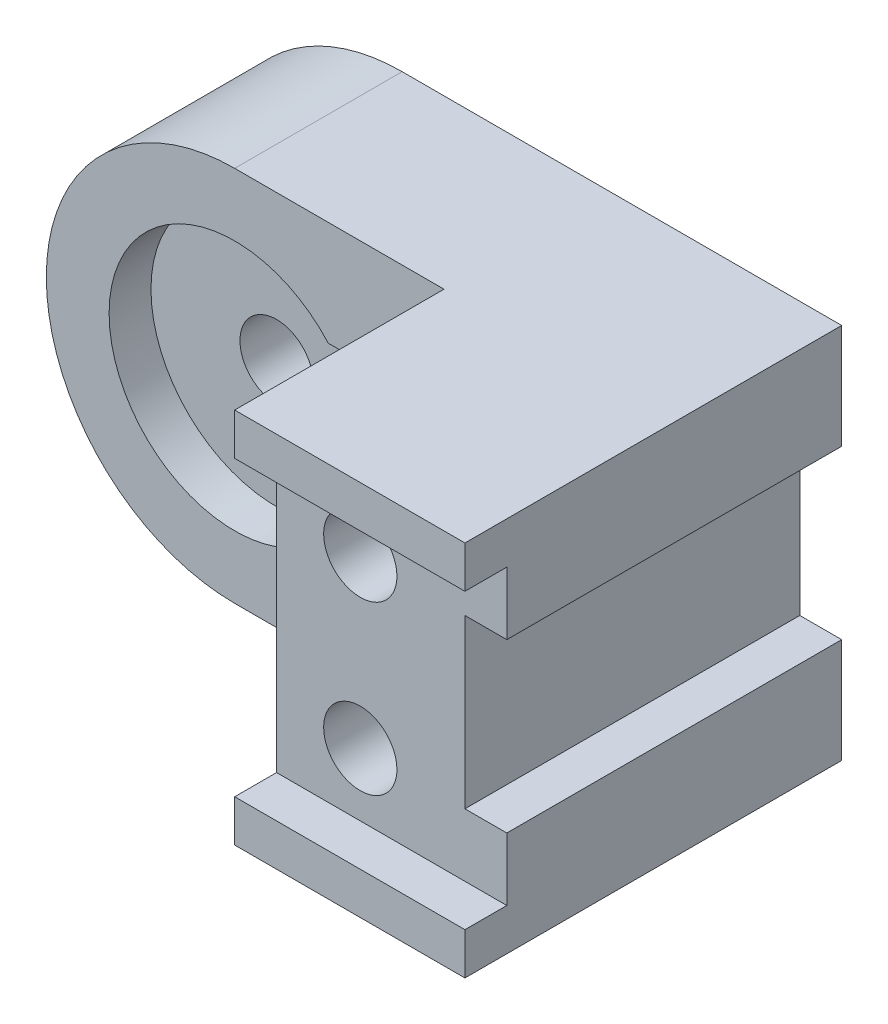
SolidWorks part; units mm, degrees
ref_plane "Front Plane" through (0, 0, 0) normal (0, 0, 1) x (1, 0, 0)
ref_plane "Top Plane" through (0, 0, 0) normal (0, 1, 0) x (1, 0, 0)
ref_plane "Right Plane" through (0, 0, 0) normal (1, 0, 0) x (0, 0, -1)
sketch "Sketch1" plane through (0, 0, 0) normal (0, 0, 1) x (1, 0, 0)
  line L1 (0, 0) -> (150, 0)
  line L2 (0, 0) -> (0, 90)
  line L3 (0, 90) -> (150, 90)
  line L4 (150, 0) -> (150, 90)
  dimension "D1" = 150
  dimension "D2" = 90
extrude "Boss-Extrude1" add sketch "Sketch1" along normal blind 90
sketch "Sketch2" plane through (0, 0, 90) normal (0, 0, 1) x (1, 0, 0)
  line L0 (150, 0) -> (150, 90) construction
  line L1 (150, 65) -> (140, 65)
  line L2 (150, 65) -> (150, 25)
  line L3 (150, 25) -> (140, 25)
  line L4 (140, 65) -> (140, 25)
  dimension "D1" = 10
  dimension "D2" = 40
  dimension "D3" = 25
extrude "Cut-Extrude1" cut sketch "Sketch2" against normal blind 90
sketch "Sketch3" plane through (0, 0, 90) normal (0, 0, 1) x (1, 0, 0)
  line L0 (150, 90) -> (0, 90) construction
  line L1 (45, 90) -> (0, 90)
  line L2 (0, 90) -> (0, 0)
  line L3 (0, 0) -> (45, 0)
  arc A0 (45, 90) -> (45, 0) centre (45, 45) ccw
  line M6 (150, 90) -> (0, 90)
  line M7 (0, 90) -> (0, 0)
  line M8 (0, 0) -> (150, 0)
  dimension "D2" = 45
  dimension "D1" = 45
  dimension "D3" = 45
  dimension "D4" = 45
  dimension "D5" = 90
extrude "Cut-Extrude2" cut sketch "Sketch3" against normal blind 90 contours A0 M6 M7 | A0 L2 M8
sketch "Sketch4" plane through (0, 0, 0) normal (0, 0, -1) x (-1, 0, 0)
  line L0 (-11.459, 75) -> (-45, 75)
  line L1 (-11.459, 15) -> (-45, 15)
  arc A0 (-45, 0) -> (-45, 90) centre (-45, 45) ccw construction
  circle A1 centre (-45, 45) radius 30
  arc M2 (-45, 0) -> (-45, 90) centre (-45, 45) ccw
  dimension "D1" = 15
  dimension "D2" = 15
extrude "Cut-Extrude3" cut sketch "Sketch4" against normal blind 10 contours A1 L1 L0 M2 | A1 L1
sketch "Sketch5" plane through (0, 0, 90) normal (0, 0, 1) x (1, 0, 0)
  line L0 (95, 90) -> (95, 0)
  line L1 (150, 90) -> (45, 90) construction
  line L2 (45, 0) -> (150, 0) construction
  line L3 (95, 0) -> (45, 0)
  line L4 (95, 90) -> (45, 90)
  arc A0 (45, 90) -> (45, 0) centre (45, 45) ccw
  arc A1 (45, 90) -> (45, 0) centre (45, 45) ccw construction
  dimension "D1" = 55
extrude "Cut-Extrude4" cut sketch "Sketch5" against normal blind 50
sketch "Sketch6" plane through (95, 0, 0) normal (-1, 0, 0) x (0, 0, 1)
  line L0 (90, 0) -> (90, 90) construction
  line L1 (90, 80) -> (80, 80)
  line L2 (90, 80) -> (90, 10)
  line L3 (90, 10) -> (80, 10)
  line L4 (80, 80) -> (80, 10)
  dimension "D1" = 10
  dimension "D2" = 10
  dimension "D3" = 10
extrude "Cut-Extrude6" cut sketch "Sketch6" against normal blind 94
sketch "Sketch7" plane through (0, 0, 40) normal (0, 0, 1) x (1, 0, 0)
  line L0 (67.3607, 65) -> (95, 65)
  line L1 (95, 0) -> (95, 90) construction
  line L2 (95, 65) -> (95, 25)
  line L3 (95, 25) -> (67.3607, 25)
  line L4 (45, 0) -> (95, 0) construction
  circle A0 centre (45, 45) radius 30
  line M4 (95, 0) -> (95, 90)
  dimension "D1" = 60
  dimension "D2" = 40
  dimension "D3" = 25
extrude "Cut-Extrude8" cut sketch "Sketch7" against normal blind 10 contours A0 | A0 L3 L0 M4
sketch "Sketch8" plane through (0, 0, 80) normal (0, 0, 1) x (1, 0, 0)
  point P0 (115, 65)
  point P1 (115, 25)
  dimension "D1" = 35
  dimension "D2" = 35
  dimension "D3" = 25
  dimension "D4" = 25
hole_wizard "M20 Tapped Hole2" positions "3DSketch2" profile "Sketch10" tap size "M20" standard "ISO"
sketch3d "3DSketch2"
  point P0 (115, 65, 80)
  point P3 (115, 25, 80)
sketch "Sketch10" plane through (115, 65, 80) normal (1, 0, 0) x (0, -1, 0)
  line L0 (0, 0) -> (0, 30.2575)
  line L1 (0, 30.2575) -> (8.75, 25)
  line L2 (8.75, 25) -> (8.75, 0)
  line L5 (8.75, 0) -> (0, 0)
  line L10 (0, 30.2575) -> (-8.75, 25) construction
  line L11 (0, -6.35) -> (0, 107.95) construction
  dimension "Tap Drill Dia." = 17.5
  dimension "Tap Drill Depth" = 25
  dimension "Drill Angle" = 118
cosmetic thread "Hole Thread3" parameters "D1"=25, "D2"=20
cosmetic thread "Hole Thread4" parameters "D1"=25, "D2"=20
sketch "Sketch11" plane through (0, 0, 30) normal (0, 0, 1) x (1, 0, 0)
  point P0 (45, 45)
hole_wizard "M20 Tapped Hole3" positions "3DSketch3" profile "Sketch12" tap size "M20" standard "ISO"
sketch3d "3DSketch3"
  line L0 (45, 45, 0) -> (45, 45, 40) construction
  point P0 (45, 45, 40)
sketch "Sketch12" plane through (45, 45, 40) normal (1, 0, 0) x (0, -1, 0)
  line L0 (0, 0) -> (0, 42.7575)
  line L1 (0, 42.7575) -> (8.75, 37.5)
  line L2 (8.75, 37.5) -> (8.75, 0)
  line L5 (8.75, 0) -> (0, 0)
  line L10 (0, 42.7575) -> (-8.75, 37.5) construction
  line L11 (0, -6.35) -> (0, 107.95) construction
  dimension "Tap Drill Dia." = 17.5
  dimension "Tap Drill Depth" = 37.5
  dimension "Drill Angle" = 118
cosmetic thread "Hole Thread5" parameters "D1"=30, "D2"=20
